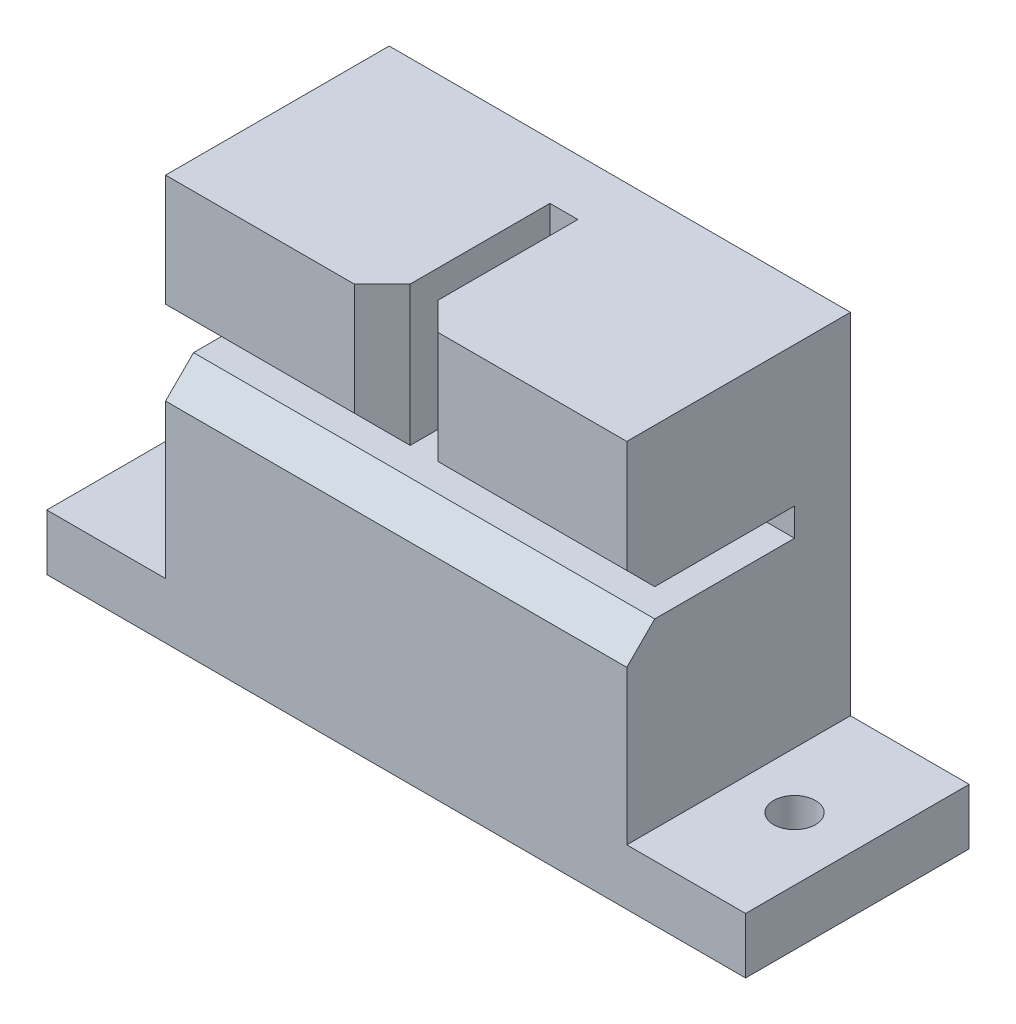
SolidWorks part; units mm, degrees
material "ABS generico"
ref_plane "Front Plane" through (0, 0, 0) normal (0, 0, 1) x (1, 0, 0)
ref_plane "Top Plane" through (0, 0, 0) normal (0, 1, 0) x (1, 0, 0)
ref_plane "Right Plane" through (0, 0, 0) normal (1, 0, 0) x (0, 0, -1)
sketch "Sketch1" plane through (0, 0, 0) normal (0, 0, 1) x (1, 0, 0)
  line L0 (-25, -14.5) -> (25, -14.5)
  line L1 (-16.5, 14.5) -> (16.5, 14.5)
  line L2 (-16.5, 14.5) -> (-16.5, -10.5)
  line L3 (-16.5, -14.5) -> (16.5, -14.5)
  line L4 (16.5, 14.5) -> (16.5, -10.5)
  line L5 (-16.5, 14.5) -> (16.5, -14.5) construction
  line L6 (-16.5, -14.5) -> (16.5, 14.5) construction
  line L7 (-25, -10.5) -> (-16.5, -10.5)
  line L8 (0, -22.0017) -> (0, 34.5889) construction
  line L9 (25, -14.5) -> (25, -10.5)
  line L10 (-25, -14.5) -> (-25, -10.5)
  line L11 (16.5, -10.5) -> (25, -10.5)
  line L12 (-25, -22.0017) -> (-25, 34.5889) construction
  line L13 (-48.5805, -10.5) -> (62.5201, -10.5) construction
  line L14 (-48.5805, -14.5) -> (62.5201, -14.5) construction
  line L16 (25, -22.0017) -> (25, 34.5889) construction
  point P0 (0, 0)
  dimension "D1" = 33
  dimension "D2" = 29
  dimension "D3" = 4
  dimension "D4" = 25
  dimension "D5" = 25
extrude "Extrude1" add sketch "Sketch1" against normal blind 16 contours L11 L4 L1 L2 L7 L10 L0 L9
sketch "Sketch2" plane through (0, 0, 0) normal (0, 0, 1) x (1, 0, 0)
  line L0 (-1, 14.5) -> (1, 14.5)
  line L1 (-16.5, 2.5) -> (16.5, 2.5)
  line L2 (-16.5, 26.5) -> (29.5295, 26.5)
  line L3 (-16.5, 4.5) -> (-1, 4.5)
  line L4 (0, 1.9361) -> (0, 14.5) construction
  line L6 (-16.5, 2.5) -> (29.5295, 2.5) construction
  line L7 (-16.5, 4.5) -> (-16.5, 2.5)
  line L8 (16.5, 4.5) -> (16.5, 2.5)
  line L10 (1, 4.5) -> (1, 14.5)
  line L11 (-16.5, 14.5) -> (29.5295, 14.5) construction
  line L15 (1, 4.5) -> (16.5, 4.5)
  line L16 (-1, 4.5) -> (-1, 14.5)
  line L17 (-16.5, 4.5) -> (29.5295, 4.5) construction
  point P10 (0, 16.737)
  point P12 (1, 1.9361)
  point P13 (1, 16.737)
  point P14 (-1, 1.9361)
  point P15 (-1, 16.737)
  line M5 (16.5, -10.5) -> (16.5, 14.5)
  line M6 (16.5, 14.5) -> (-16.5, 14.5)
  line M7 (-16.5, 14.5) -> (-16.5, -10.5)
  dimension "D1" = 12
  dimension "D2" = 2
extrude "Extrude6" cut sketch "Sketch2" against normal blind 12 contours L16 L3 L1 L15 L10 M7 M5 M6
chamfer "Chamfer1" distance 2 angle 45 5 edges at (1, 9.5, 0) (8.75, 4.5, 0) (0, 2.5, 0) (-1, 9.5, 0) (-8.75, 4.5, 0)
sketch "Sketch3" plane through (0, -14.5, 0) normal (0, -1, 0) x (1, 0, 0)
  line L0 (-25, -8) -> (25, -8) construction
  line L1 (-25, -16) -> (-25, 0) construction
  line L2 (25, -16) -> (25, 0) construction
  line L3 (0, 6.24) -> (0, -19.7792) construction
  circle A0 centre (-20.5, -8) radius 1.5
  circle A1 centre (20.5, -8) radius 1.5
  dimension "D2" = 3
  dimension "D1" = 20.5
extrude "Extrude7" cut sketch "Sketch3" against normal up to surface (4 mm away) up to face at (20.75, -10.5, -8)
